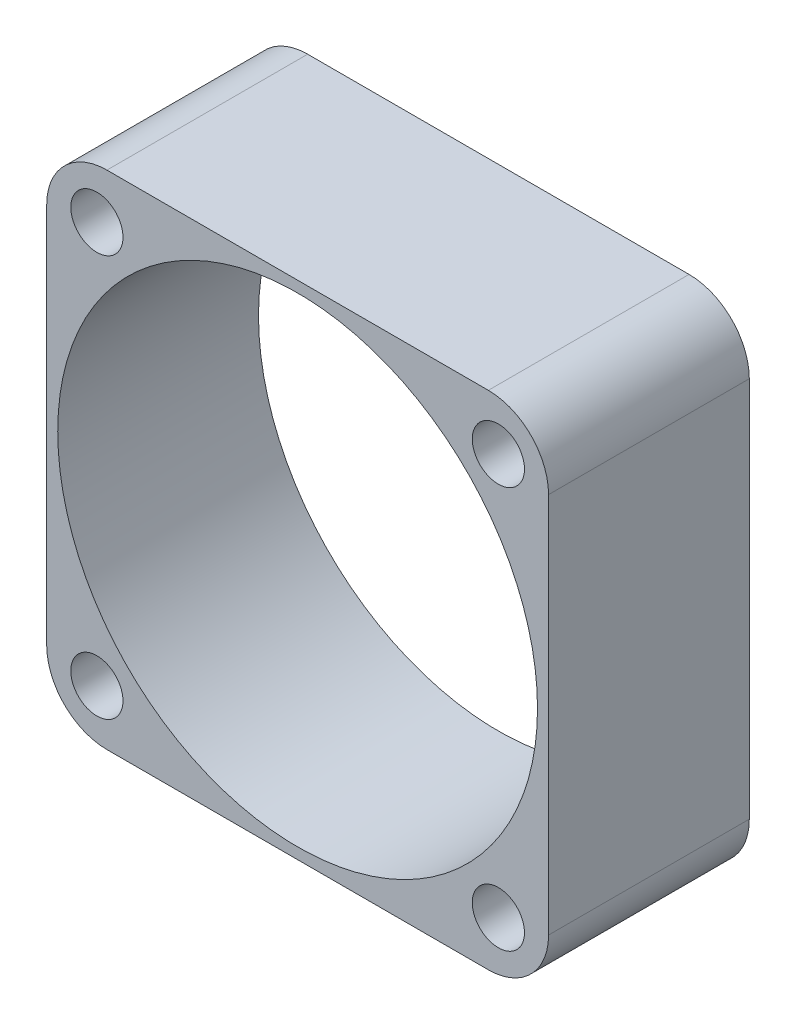
SolidWorks part; units mm, degrees
ref_plane "Plano frontal" through (0, 0, 0) normal (0, 0, 1) x (1, 0, 0)
ref_plane "Plano superior" through (0, 0, 0) normal (0, 1, 0) x (1, 0, 0)
ref_plane "Plano direito" through (0, 0, 0) normal (1, 0, 0) x (0, 0, -1)
sketch "Sketch1" plane through (0, 0, 0) normal (0, 0, 1) x (1, 0, 0)
  line L1 (-12.8242, -87.6141) -> (-37.8242, -87.6141)
  line L2 (-12.8242, -87.6141) -> (-12.8242, -62.6141)
  line L3 (-12.8242, -62.6141) -> (-37.8242, -62.6141)
  line L4 (-37.8242, -87.6141) -> (-37.8242, -62.6141)
  dimension "D1" = 25
  dimension "D2" = 25
extrude "Boss-Extrude1" add sketch "Sketch1" along normal blind 10
fillet "Fillet1" radius 3 4 edges at (-12.8242, -87.6141, 5) (-12.8242, -62.6141, 5) (-37.8242, -62.6141, 5) (-37.8242, -87.6141, 5)
sketch "Sketch2" plane through (0, 0, 10) normal (0, 0, 1) x (1, 0, 0)
  line L0 (-25.3242, -65.1141) -> (-25.3242, -85.1141) construction
  line L1 (-35.3242, -65.1141) -> (-15.3242, -65.1141) construction
  line L2 (-35.3242, -65.1141) -> (-35.3242, -85.1141) construction
  line L3 (-35.3242, -85.1141) -> (-15.3242, -85.1141) construction
  line L4 (-15.3242, -65.1141) -> (-15.3242, -85.1141) construction
  line L5 (-35.3242, -75.1141) -> (-15.3242, -75.1141) construction
  line L6 (-25.3242, -62.6141) -> (-25.3242, -87.5132) construction
  line L7 (-15.8242, -62.6141) -> (-34.8242, -62.6141) construction
  line L8 (-12.8242, -75.1141) -> (-37.8242, -75.1141) construction
  line L9 (-12.8242, -84.6141) -> (-12.8242, -65.6141) construction
  line L10 (-37.8242, -65.6141) -> (-37.8242, -84.6141) construction
  circle A0 centre (-35.3242, -65.1141) radius 1.3
  circle A1 centre (-15.3242, -65.1141) radius 1.3
  circle A2 centre (-15.3242, -85.1141) radius 1.3
  circle A3 centre (-35.3242, -85.1141) radius 1.3
  point P22 (-25.3242, -75.1141)
  point P23 (-25.3242, -75.0636)
  dimension "D3" = 2.6
  dimension "D4" = 2.6
  dimension "D5" = 2.6
  dimension "D6" = 2.6
  dimension "D1" = 20
  dimension "D2" = 20
extrude "Cut-Extrude1" cut sketch "Sketch2" against normal blind 10 contours A2 | A1 | A0 | A3
sketch "Sketch3" plane through (0, 0, 10) normal (0, 0, 1) x (1, 0, 0)
  circle A0 centre (-25.3242, -75.1141) radius 11.95
  dimension "D1" = 23.9
extrude "Cut-Extrude2" cut sketch "Sketch3" against normal blind 10
